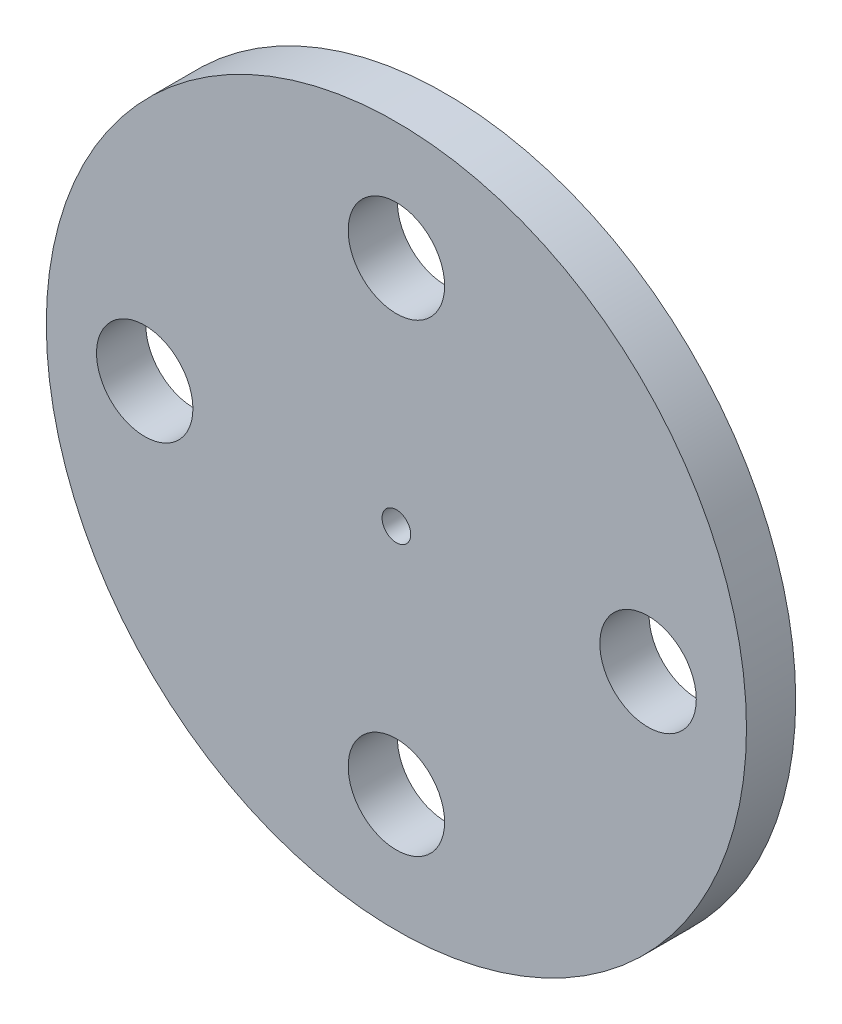
SolidWorks part; units mm, degrees
ref_plane "Front Plane" through (0, 0, 0) normal (0, 0, 1) x (1, 0, 0)
ref_plane "Top Plane" through (0, 0, 0) normal (0, 1, 0) x (1, 0, 0)
ref_plane "Right Plane" through (0, 0, 0) normal (1, 0, 0) x (0, 0, -1)
sketch "Sketch1" plane through (0, 0, 0) normal (0, 0, 1) x (1, 0, 0)
  line L0 (0, 22.6143) -> (0, -22.6143) construction
  circle A3 centre (0, 0) radius 22.6143
  circle A4 centre (0, 0) radius 0.925
  circle A5 centre (-16.2559, 0) radius 3.1128
  circle A6 centre (0, -15) radius 3.115
  circle A7 centre (16.2559, 0) radius 3.115
  circle A8 centre (0, 15) radius 3.115
  dimension "D1" = 1.85
  dimension "D2" = 6.2256
  dimension "D3" = 6.23
  dimension "D4" = 6.23
  dimension "D5" = 6.23
extrude "Boss-Extrude5" add sketch "Sketch1" along normal blind 3.18
